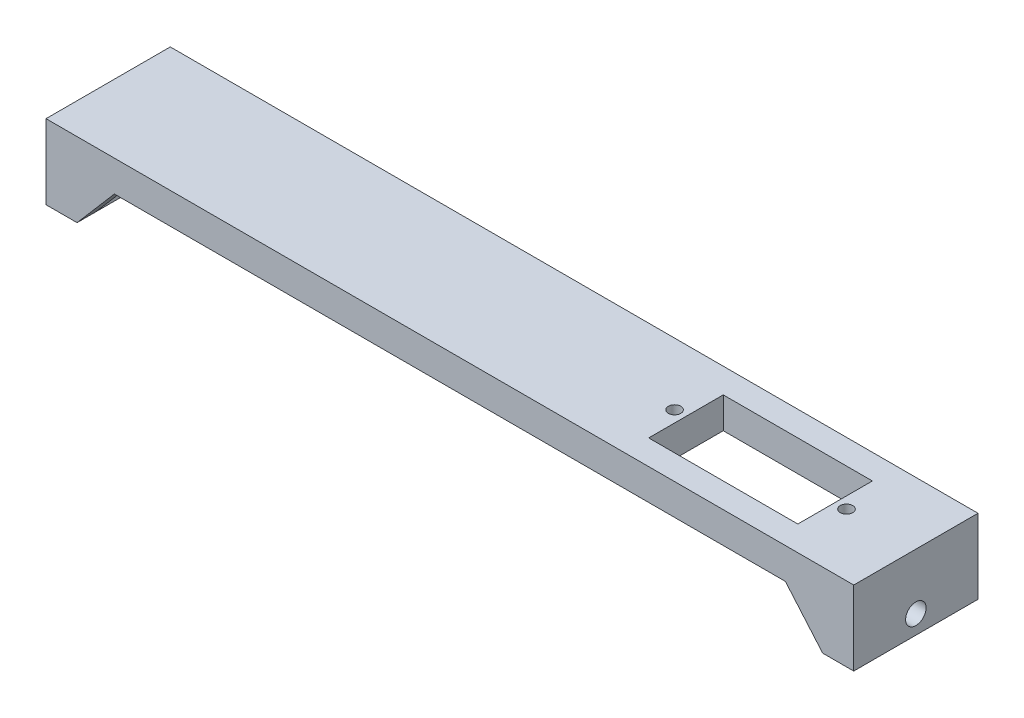
SolidWorks part; units mm, degrees
ref_plane "前视基准面" through (0, 0, 0) normal (0, 0, 1) x (1, 0, 0)
ref_plane "上视基准面" through (0, 0, 0) normal (0, 1, 0) x (1, 0, 0)
ref_plane "右视基准面" through (0, 0, 0) normal (1, 0, 0) x (0, 0, -1)
sketch "草图1" plane through (0, 0, 0) normal (0, 0, 1) x (1, 0, 0)
  line L0 (-65, 0) -> (65, 0)
  line L1 (65, 0) -> (65, -12)
  line L2 (65, -12) -> (60, -12)
  line L3 (60, -12) -> (60, -5)
  line L4 (60, -5) -> (-60, -5)
  line L5 (-60, -5) -> (-60, -12)
  line L6 (-60, -12) -> (-65, -12)
  line L7 (-65, -12) -> (-65, 0)
  line L8 (0, -7.4248) -> (0, 9.2484) construction
  dimension "D1" = 5
  dimension "D2" = 5
  dimension "D3" = 130
  dimension "D4" = 12
  dimension "D5" = 12
extrude "凸台-拉伸2" add sketch "草图1" along normal blind 20
sketch "草图3" plane through (-60, 0, 0) normal (1, 0, 0) x (0, 0, -1)
  line L0 (0, 0) -> (0, -12) construction
  line L1 (-20, -12) -> (0, -12) construction
  circle A0 centre (-10, -9) radius 1.65
  dimension "D2" = 3.3
  dimension "D1" = 3
  dimension "D3" = 10
extrude "切除-拉伸1" cut sketch "草图3" against normal through all both and the other way through all
sketch "草图4" plane through (0, 0, 0) normal (0, 0, -1) x (-1, 0, 0)
  line L0 (54, -5) -> (60, -12)
  line L1 (60, -5) -> (-60, -5) construction
  line L2 (54, -5) -> (60, -5)
  line L4 (60, -5) -> (60, -12)
  dimension "D1" = 6
extrude "凸台-拉伸3" add sketch "草图4" against normal blind 3
sketch "草图5" plane through (0, -5, 0) normal (0, -1, 0) x (1, 0, 0)
  line L0 (60, 10) -> (-60, 10) construction
  line L1 (60, 20) -> (60, 0) construction
  line L2 (-60, 20) -> (-60, 3) construction
ref_plane "基准面3" through (0, 0, 10) normal (0, 0, 1) x (1, 0, 0)
mirror "镜向1" about plane through (0, 0, 10) normal (0, 0, 1) of "凸台-拉伸3"
sketch "草图6" plane through (0, 0, 0) normal (0, 1, 0) x (1, 0, 0)
  line L0 (0, -20) -> (0, 0) construction
  line L1 (65, -20) -> (-65, -20) construction
mirror "镜向2" about plane through (0, 0, 0) normal (1, 0, 0) of "镜向1", "凸台-拉伸3"
sketch "草图7" plane through (0, -5, 0) normal (0, -1, 0) x (1, 0, 0)
  line L0 (60, 10) -> (-60, 10) construction
  line L1 (52, 4) -> (28, 4)
  line L2 (52, 4) -> (52, 16)
  line L3 (52, 16) -> (28, 16)
  line L4 (28, 4) -> (28, 16)
  line L5 (52, 4) -> (28, 16) construction
  line L6 (52, 16) -> (28, 4) construction
  line L8 (65, 20) -> (65, 0) construction
  point P0 (40, 10)
  dimension "D1" = 12
  dimension "D2" = 24
  dimension "D3" = 25
extrude "切除-拉伸2" cut sketch "草图7" against normal blind 5 contours L1 L4 L3 L2
sketch "草图10" plane through (0, -5, 0) normal (0, -1, 0) x (1, 0, 0)
  line L0 (40, 16) -> (40, 4) construction
  line L1 (52, 16) -> (28, 16) construction
  line L2 (52, 4) -> (28, 4) construction
  line L3 (65, 20) -> (-65, 20) construction
  circle A0 centre (53.835, 10) radius 1
  circle A1 centre (26.165, 10) radius 1
  point P10 (40, 10)
  dimension "D2" = 2
  dimension "D3" = 10
  dimension "D1" = 13.835
extrude "切除-拉伸3" cut sketch "草图10" against normal blind 5
